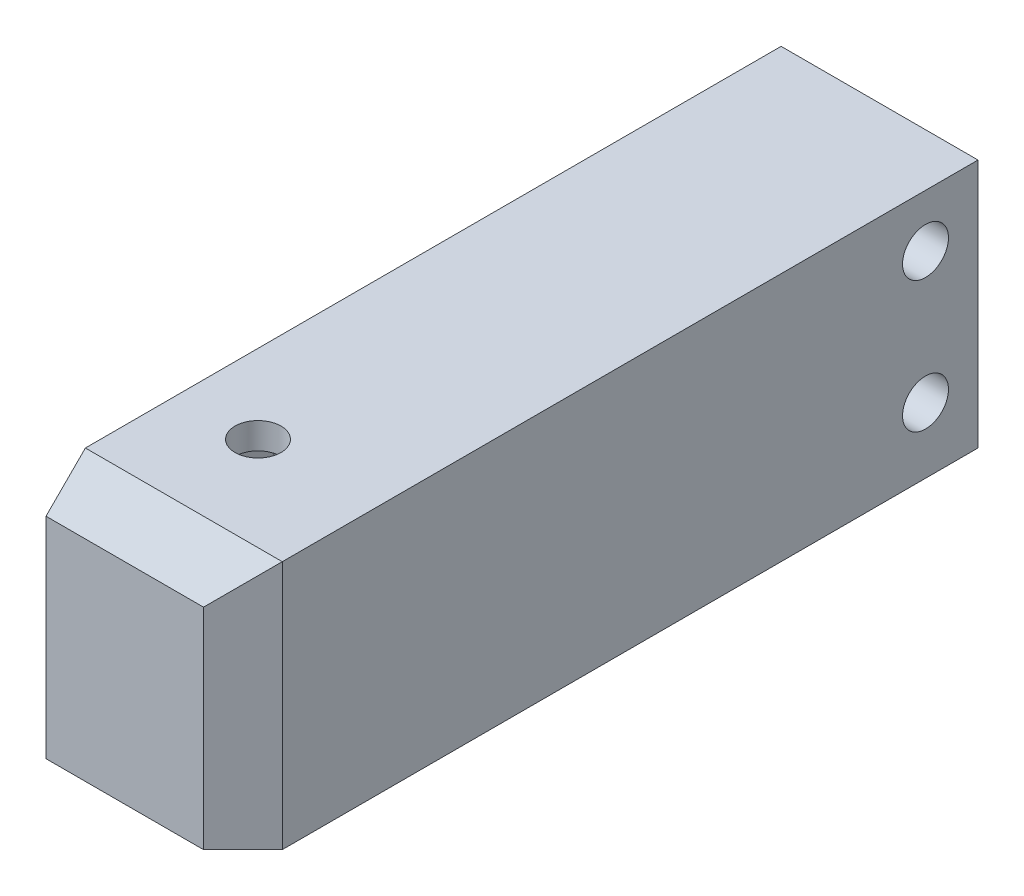
SolidWorks part; units mm, degrees
ref_plane "Alzado" through (0, 0, 0) normal (0, 0, 1) x (1, 0, 0)
ref_plane "Planta" through (0, 0, 0) normal (0, 1, 0) x (1, 0, 0)
ref_plane "Vista lateral" through (0, 0, 0) normal (1, 0, 0) x (0, 0, -1)
ref_plane "Plano1" through (-177, 0, 0) normal (-1, 0, 0) x (0, -1, 0)
sketch "Croquis1" plane through (-177, 0, 0) normal (-1, 0, 0) x (0, -1, 0)
  line L0 (-47, 82.5) -> (-47, 138.5)
  line L1 (-47, 138.5) -> (-66, 138.5)
  line L2 (-66, 138.5) -> (-66, 82.5)
  line L3 (-66, 82.5) -> (-47, 82.5)
extrude "Saliente-Extruir1" add sketch "Croquis1" against normal blind 15
chamfer "Chaflán1" distance 3 angle 45 2 edges at (-162, 56.5, 138.5) (-169.5, 66, 138.5)
sketch "Croquis2" plane through (0, 47, 0) normal (0, -1, 0) x (1, 0, 0)
  line L0 (-177, 134.5) -> (-177, 110.5)
  line L1 (-177, 110.5) -> (-164.5, 110.5)
  line L2 (-164.5, 110.5) -> (-164.5, 134.5)
  line L3 (-164.5, 134.5) -> (-177, 134.5)
extrude "Cortar-Extruir1" cut sketch "Croquis2" against normal blind 15
sketch "Croquis3" plane through (0, 47, 0) normal (0, -1, 0) x (1, 0, 0)
  circle A0 centre (-171, 136.25) radius 1
extrude "Cortar-Extruir2" cut sketch "Croquis3" against normal blind 15
ref_plane "Plano2" through (0, 47, 0) normal (0, -1, 0) x (-1, 0, 0)
sketch "Croquis8" plane through (0, 47, 0) normal (0, -1, 0) x (-1, 0, 0)
  circle A0 centre (171, -108.75) radius 1
extrude "Cortar-Extruir3" cut sketch "Croquis8" against normal blind 15
sketch "Croquis9" plane through (-162, 0, 0) normal (1, 0, 0) x (0, 0, -1)
  circle A0 centre (-86.5, 52) radius 1.75
extrude "Cortar-Extruir4" cut sketch "Croquis9" against normal through all
sketch "Croquis10" plane through (-162, 0, 0) normal (1, 0, 0) x (0, 0, -1)
  circle A0 centre (-86.5, 62) radius 1.75
extrude "Cortar-Extruir5" cut sketch "Croquis10" against normal up to next
sketch "Croquis11" plane through (0, 66, 0) normal (0, 1, 0) x (-1, 0, 0)
  circle A0 centre (171, 128.35) radius 1.75
extrude "Cortar-Extruir6" cut sketch "Croquis11" against normal through all
sketch "Croquis12" plane through (0, 62, 0) normal (0, -1, 0) x (1, 0, 0)
  line L0 (-172.65, 125.4921) -> (-169.35, 125.4921)
  line L1 (-169.35, 125.4921) -> (-167.7, 128.35)
  line L2 (-167.7, 128.35) -> (-169.35, 131.2079)
  line L3 (-169.35, 131.2079) -> (-172.65, 131.2079)
  line L4 (-172.65, 131.2079) -> (-174.3, 128.35)
  line L5 (-174.3, 128.35) -> (-172.65, 125.4921)
  circle A0 centre (-171, 128.35) radius 1.75
extrude "Cortar-Extruir7" cut sketch "Croquis12" against normal blind 2
